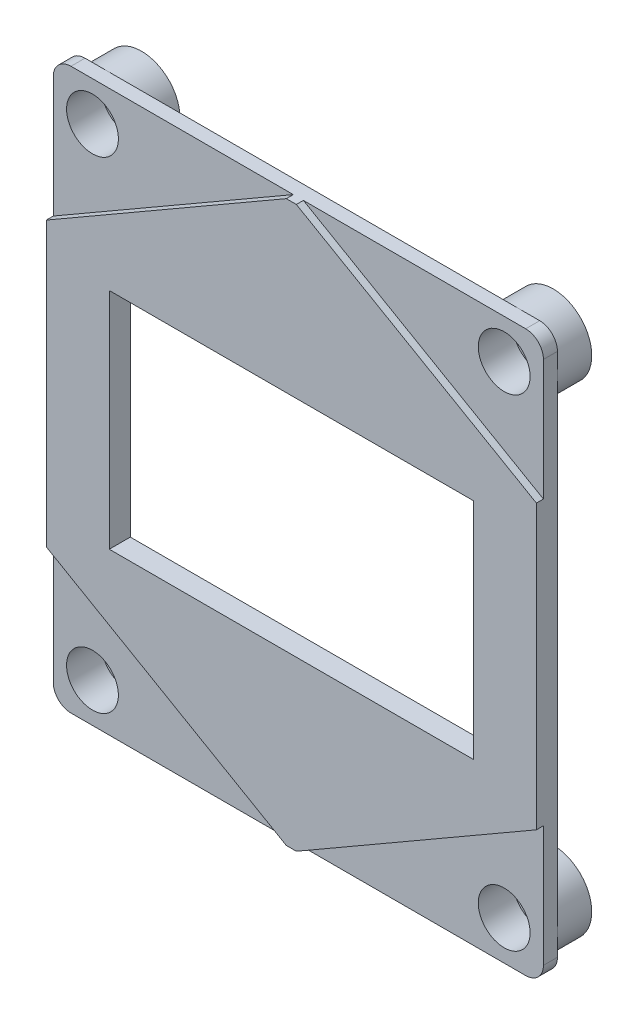
SolidWorks part; units mm, degrees
ref_plane "前视基准面" through (0, 0, 0) normal (0, 0, 1) x (1, 0, 0)
ref_plane "上视基准面" through (0, 0, 0) normal (0, 1, 0) x (1, 0, 0)
ref_plane "右视基准面" through (0, 0, 0) normal (1, 0, 0) x (0, 0, -1)
sketch "草图1" plane through (0, 0, 0) normal (0, 0, 1) x (1, 0, 0)
  line L1 (17.5, -20) -> (-17.5, -20)
  line L2 (17.5, -20) -> (17.5, 20)
  line L3 (17.5, 20) -> (-17.5, 20)
  line L4 (-17.5, -20) -> (-17.5, 20)
  line L5 (17.5, -20) -> (-17.5, 20) construction
  line L6 (17.5, 20) -> (-17.5, -20) construction
  point P0 (0, 0)
  dimension "D1" = 35
  dimension "D2" = 40
extrude "凸台-拉伸1" add sketch "草图1" along normal blind 1
sketch "草图2" plane through (0, 0, 0) normal (0, 0, -1) x (-1, 0, 0)
  line L0 (0, 0) -> (-20.4357, 0) construction
  line L1 (0, 0) -> (0, 21.7058) construction
  circle A0 centre (-14.7, 17.2) radius 2.75
  dimension "D1" = 5.5
  dimension "D2" = 14.7
  dimension "D3" = 17.2
extrude "凸台-拉伸2" add sketch "草图2" along normal blind 2.5
sketch "草图3" plane through (0, 0, 1) normal (0, 0, 1) x (1, 0, 0)
  line L0 (0, 0) -> (0, 22.1068) construction
  line L1 (0, 0) -> (17.5, 0) construction
  line L2 (17.5, -20) -> (17.5, 20) construction
  circle A0 centre (14.7, 17.2) radius 1.85
  dimension "D3" = 3.7
  dimension "D1" = 14.7
  dimension "D2" = 17.2
extrude "切除-拉伸1" cut sketch "草图3" against normal blind 2.5
sketch "草图4" plane through (0, 0, -2.5) normal (0, 0, -1) x (-1, 0, 0)
  circle A0 centre (-14.7, 17.2) radius 1.1
  dimension "D1" = 2.2
extrude "切除-拉伸2" cut sketch "草图4" against normal mid plane 4
sketch "草图5" plane through (0, 0, 1) normal (0, 0, 1) x (1, 0, 0)
  line L0 (-17.5, -20) -> (17.5, -20) construction
  line L1 (-13, 8) -> (13, 8)
  line L2 (-13, 8) -> (-13, -8)
  line L3 (-13, -8) -> (13, -8)
  line L4 (13, 8) -> (13, -8)
  line L5 (17.5, 20) -> (-17.5, 20) construction
  line L6 (17.5, -20) -> (17.5, 20) construction
  line L7 (-17.5, 20) -> (-17.5, -20) construction
  point P6 (0, -20)
  point P9 (0, 20)
  dimension "D1" = 12
  dimension "D2" = 12
  dimension "D3" = 4.5
  dimension "D4" = 4.5
ref_plane "基准面1" through (0, 0, 25.2921) normal (0, 0, 1) x (1, 0, 0)
fillet "圆角1" radius 1.265 4 edges at (-17.5, -20, 0.5) (17.5, -20, 0.5) (17.5, 20, 0.5) (-17.5, 20, 0.5)
mirror "镜向8" about plane through (0, 0, 0) normal (1, 0, 0) of "凸台-拉伸2"
mirror "镜向9" about plane through (0, 0, 0) normal (0, 1, 0) of "镜向8", "凸台-拉伸2"
mirror "镜向10" about plane through (0, 0, 0) normal (0, 1, 0) of "切除-拉伸2"
mirror "镜向11" about plane through (0, 0, 0) normal (1, 0, 0) of "镜向10", "切除-拉伸2"
mirror "镜向12" about plane through (0, 0, 0) normal (1, 0, 0) of "切除-拉伸1"
mirror "镜向13" about plane through (0, 0, 0) normal (0, 1, 0) of "镜向12", "切除-拉伸1"
extrude "切除-拉伸3" cut sketch "草图5" against normal mid plane 10
sketch "草图10" plane through (0, 0, 1) normal (0, 0, 1) x (1, 0, 0)
  line L0 (-13, 8) -> (13, 8) construction
  line L1 (13, 8) -> (22.0976, 8) construction
  line L2 (13, 8) -> (13, 21.7151) construction
  line L4 (0, 20.2073) -> (-17.5, 10.1036)
  line L5 (-17.5, 10.1036) -> (-17.5, -10.1036)
  line L6 (-17.5, -10.1036) -> (0, -20.2073)
  line L7 (0, -20.2073) -> (17.5, -10.1036)
  line L8 (17.5, -10.1036) -> (17.5, 10.1036)
  line L9 (17.5, 10.1036) -> (0, 20.2073)
  circle A0 centre (0, 0) radius 17.5 construction
  point P7 (0, 0)
  point P16 (0, 20.5885)
  dimension "D1" = 17.5
extrude "凸台-拉伸16" add sketch "草图10" along normal blind 0.5
sketch "草图11" plane through (0, 0, 1) normal (0, 0, -1) x (-1, 0, 0)
  line L1 (-13, 8) -> (13, 8)
  line L2 (-13, 8) -> (-13, -8)
  line L3 (-13, -8) -> (13, -8)
  line L4 (13, 8) -> (13, -8)
extrude "切除-拉伸4" cut sketch "草图11" against normal blind 5
sketch "草图12" plane through (0, 0, 1) normal (0, 0, -1) x (-1, 0, 0)
  line L0 (-0.359, 20) -> (0.359, 20)
  line L1 (0.359, 20) -> (0, 20.2073)
  line L2 (0, 20.2073) -> (-0.359, 20)
extrude "切除-拉伸5" cut sketch "草图12" against normal blind 5
mirror "镜向15" about plane through (0, 0, 0) normal (0, 1, 0) of "切除-拉伸5"
